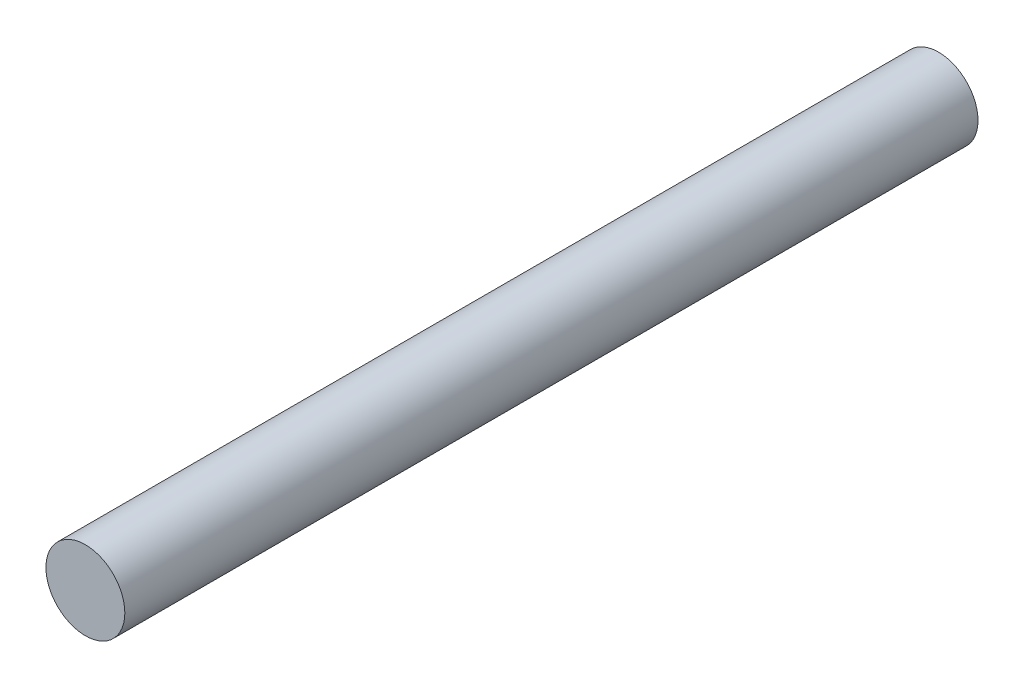
SolidWorks part; units mm, degrees
ref_plane "Front Plane" through (0, 0, 0) normal (0, 0, 1) x (1, 0, 0)
ref_plane "Top Plane" through (0, 0, 0) normal (0, 1, 0) x (1, 0, 0)
ref_plane "Right Plane" through (0, 0, 0) normal (1, 0, 0) x (0, 0, -1)
sketch "Sketch1" plane through (0, 0, 0) normal (0, 0, 1) x (1, 0, 0)
  circle A0 centre (0, 0) radius 4.6248
extrude "Boss-Extrude1" add sketch "Sketch1" along normal blind 100
